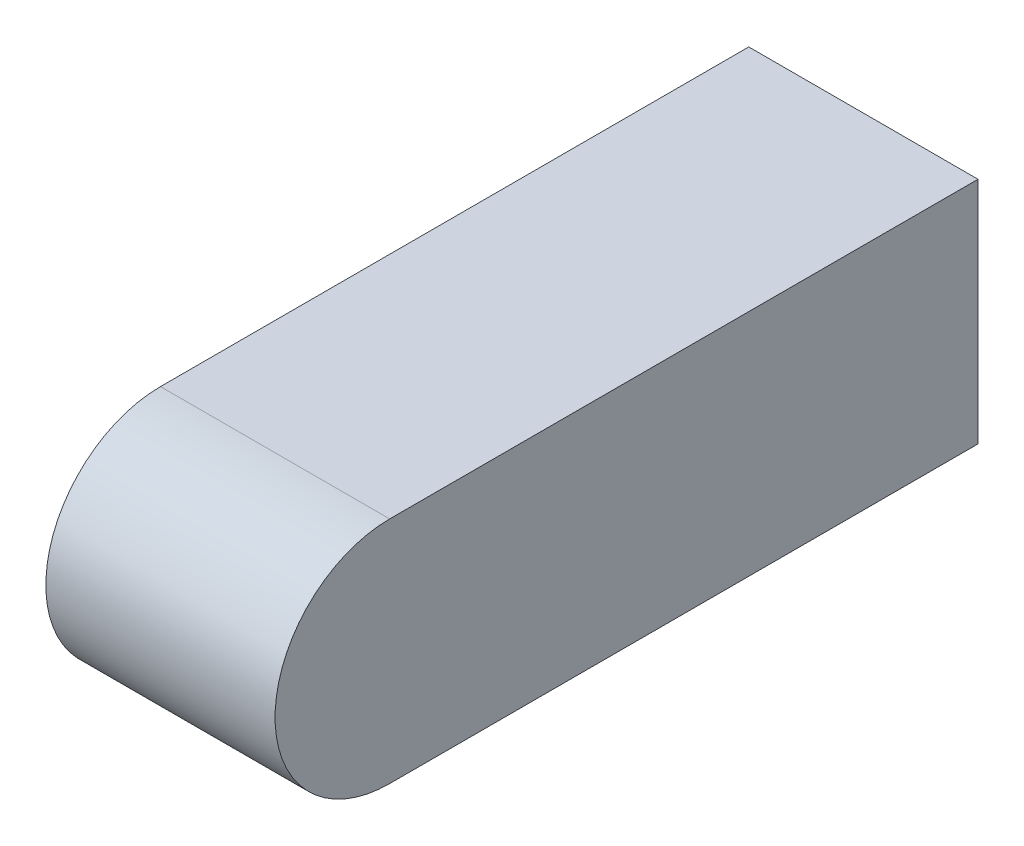
SolidWorks part; units mm, degrees
ref_plane "Front Plane" through (0, 0, 0) normal (0, 0, 1) x (1, 0, 0)
ref_plane "Top Plane" through (0, 0, 0) normal (0, 1, 0) x (1, 0, 0)
ref_plane "Right Plane" through (0, 0, 0) normal (1, 0, 0) x (0, 0, -1)
sketch "Sketch1" plane through (0, 0, 0) normal (0, 0, 1) x (1, 0, 0)
  line L1 (22.5, 22.5) -> (-22.5, 22.5)
  line L2 (22.5, 22.5) -> (22.5, -22.5)
  line L3 (22.5, -22.5) -> (-22.5, -22.5)
  line L4 (-22.5, 22.5) -> (-22.5, -22.5)
  line L5 (22.5, 22.5) -> (-22.5, -22.5) construction
  line L6 (22.5, -22.5) -> (-22.5, 22.5) construction
  point P0 (0, 0)
  dimension "D1" = 45
extrude "Boss-Extrude1" add sketch "Sketch1" along normal blind 138
sketch "Sketch2" plane through (0, 0, 0) normal (1, 0, 0) x (0, 0, -1)
  line L0 (-138, 22.5) -> (0, 22.5) construction
  line L1 (-138, -22.5) -> (0, -22.5) construction
  line L2 (-138, -22.5) -> (-138, 22.5) construction
  line L3 (-115.5, -22.5) -> (-138, -22.5)
  line L4 (-138, -22.5) -> (-138, 22.5)
  line L5 (-138, 22.5) -> (-115.5, 22.5)
  circle A0 centre (-115.5, 0) radius 22.5
extrude "Cut-Extrude1" cut sketch "Sketch2" against normal through all and the other way through all contours A0 L5 L4 | A0 L4 L3
